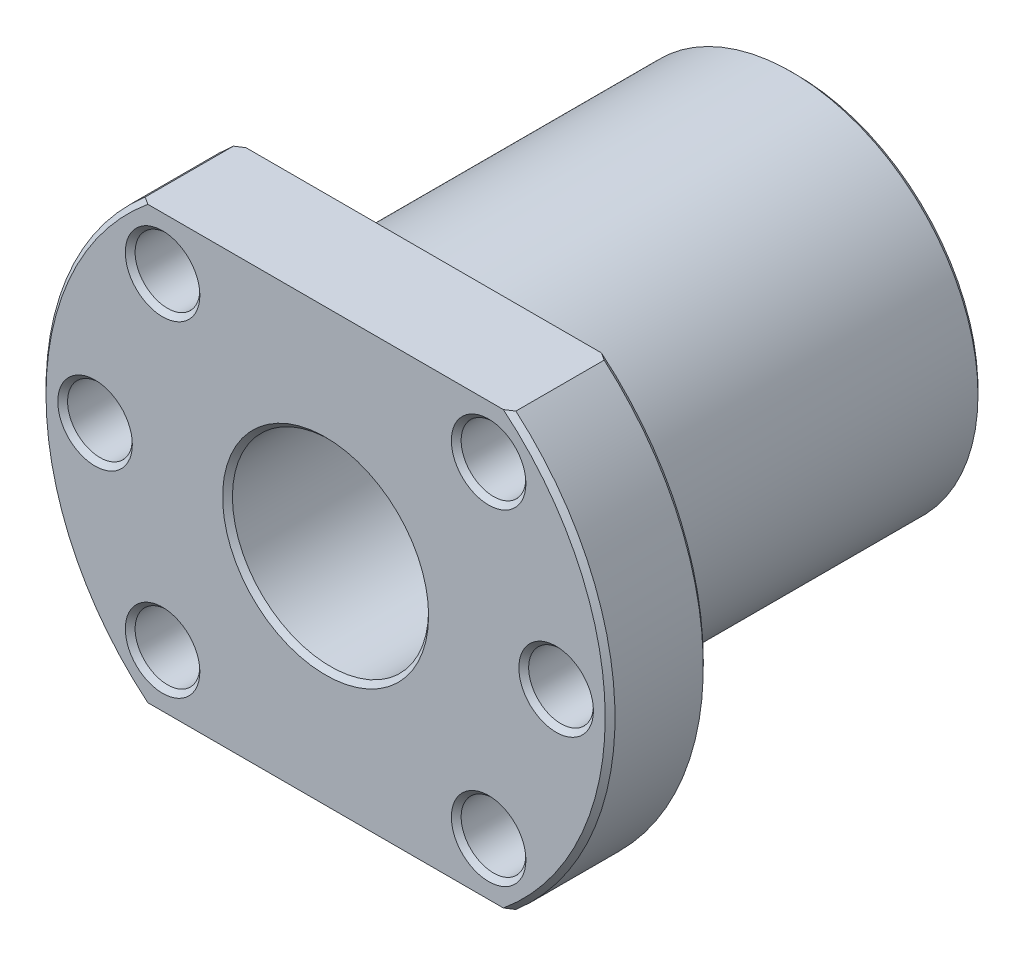
SolidWorks part; units mm, degrees
ref_plane "Płaszczyzna przednia" through (0, 0, 0) normal (0, 0, 1) x (1, 0, 0)
ref_plane "Płaszczyzna górna" through (0, 0, 0) normal (0, 1, 0) x (1, 0, 0)
ref_plane "Płaszczyzna prawa" through (0, 0, 0) normal (1, 0, 0) x (0, 0, -1)
sketch "Szkic1" plane through (0, 0, 0) normal (0, 0, 1) x (1, 0, 0)
  line L0 (-23.5, 0) -> (0, 0) construction
  line L1 (0, 0) -> (-16.617, 16.617) construction
  line L2 (0, 0) -> (-16.617, -16.617) construction
  line L3 (0, 0) -> (23.5, 0) construction
  line L4 (0, 0) -> (16.617, 16.617) construction
  line L5 (0, 0) -> (16.617, -16.617) construction
  line L6 (0, 0) -> (0, -22) construction
  line L7 (0, -22) -> (-18.8944, -22)
  line L8 (0, -22) -> (18.8944, -22)
  line L9 (0, 0) -> (0, 22) construction
  line L10 (0, 22) -> (18.8944, 22)
  line L11 (0, 22) -> (-18.8944, 22)
  arc A0 (18.8944, -22) -> (18.8944, 22) centre (0, 0) ccw
  circle A1 centre (0, 0) radius 10
  circle A2 centre (0, 0) radius 23.5 construction
  circle A3 centre (-16.617, 16.617) radius 3.3
  circle A4 centre (-23.5, 0) radius 3.3
  circle A5 centre (-16.617, -16.617) radius 3.3
  circle A6 centre (16.617, -16.617) radius 3.3
  circle A7 centre (23.5, 0) radius 3.3
  circle A8 centre (16.617, 16.617) radius 3.3
  arc A9 (-18.8944, 22) -> (-18.8944, -22) centre (0, 0) ccw
  dimension "D1" = 58
  dimension "D2" = 20
  dimension "D3" = 45
  dimension "D7" = 6.6
  dimension "D8" = 47
  dimension "D4" = 45
  dimension "D5" = 45
  dimension "D6" = 45
  dimension "D9" = 22
  dimension "D10" = 22
extrude "Dodanie-wyciągnięcie1" add sketch "Szkic1" along normal blind 10
sketch "Szkic2" plane through (0, 0, 0) normal (0, 0, -1) x (-1, 0, 0)
  circle A0 centre (0, 0) radius 10
  circle A1 centre (0, 0) radius 19
extrude "Dodanie-wyciągnięcie2" add sketch "Szkic2" along normal blind 38
chamfer "Sfazowanie1" distance 0.5 angle 45 12 edges at (26.8, 0, 10) (19.917, -16.617, 10) (-13.317, -16.617, 10) (-20.2, 0, 10) (-13.317, 16.617, 10) (19.917, 16.617, 10) (19.917, 16.617, 0) (26.8, 0, 0) (-13.317, 16.617, 0) (-20.2, 0, 0) (-13.317, -16.617, 0) (19.917, -16.617, 0)
chamfer "Sfazowanie2" distance 0.5 angle 45 7 edges at (-19, 0, -38) (-10, 0, -38) (-29, 0, 0) (29, 0, 0) (29, 0, 10) (-29, 0, 10) (10, 0, 10)
